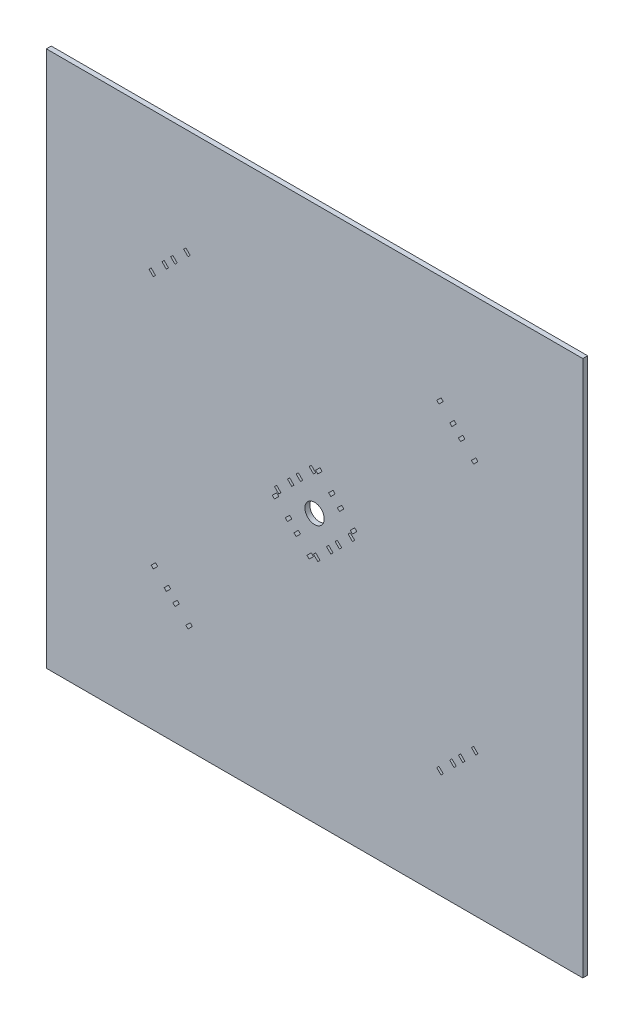
SolidWorks part; units mm, degrees
ref_plane "Front Plane" through (0, 0, 0) normal (0, 0, 1) x (1, 0, 0)
ref_plane "Top Plane" through (0, 0, 0) normal (0, 1, 0) x (1, 0, 0)
ref_plane "Right Plane" through (0, 0, 0) normal (1, 0, 0) x (0, 0, -1)
sketch "Model" plane through (0, 0, 0) normal (0, 0, 1) x (1, 0, 0)
  line L0 (0, 0) -> (0, 175)
  line L1 (0, 175) -> (175, 175)
  line L2 (175, 175) -> (175, 0)
  line L3 (175, 0) -> (0, 0)
  line L4 (139.3817, 47.6391) -> (140.7959, 46.2249)
  line L5 (140.7959, 46.2249) -> (140.0888, 45.5178)
  line L6 (140.0888, 45.5178) -> (138.6746, 46.932)
  line L7 (138.6746, 46.932) -> (139.3817, 47.6391)
  line L8 (135.1391, 43.3964) -> (136.5533, 41.9822)
  line L9 (136.5533, 41.9822) -> (135.8462, 41.2751)
  line L10 (135.8462, 41.2751) -> (134.432, 42.6893)
  line L11 (134.432, 42.6893) -> (135.1391, 43.3964)
  line L12 (132.3107, 40.568) -> (133.7249, 39.1538)
  line L13 (133.7249, 39.1538) -> (133.0178, 38.4467)
  line L14 (133.0178, 38.4467) -> (131.6036, 39.8609)
  line L15 (131.6036, 39.8609) -> (132.3107, 40.568)
  line L16 (128.068, 36.3254) -> (129.4822, 34.9112)
  line L17 (129.4822, 34.9112) -> (128.7751, 34.2041)
  line L18 (128.7751, 34.2041) -> (127.3609, 35.6183)
  line L19 (127.3609, 35.6183) -> (128.068, 36.3254)
  line L20 (87.8536, 76.5398) -> (89.2678, 75.1256)
  line L21 (89.2678, 75.1256) -> (88.5607, 74.4185)
  line L22 (88.5607, 74.4185) -> (87.1464, 75.8327)
  line L23 (87.1464, 75.8327) -> (87.8536, 76.5398)
  line L24 (92.0962, 80.7825) -> (93.5104, 79.3683)
  line L25 (93.5104, 79.3683) -> (92.8033, 78.6612)
  line L26 (92.8033, 78.6612) -> (91.3891, 80.0754)
  line L27 (91.3891, 80.0754) -> (92.0962, 80.7825)
  line L28 (47.6391, 35.6183) -> (46.2249, 34.2041)
  line L29 (46.2249, 34.2041) -> (45.5178, 34.9112)
  line L30 (45.5178, 34.9112) -> (46.932, 36.3254)
  line L31 (46.932, 36.3254) -> (47.6391, 35.6183)
  line L32 (43.3964, 39.8609) -> (41.9822, 38.4467)
  line L33 (41.9822, 38.4467) -> (41.2751, 39.1538)
  line L34 (41.2751, 39.1538) -> (42.6893, 40.568)
  line L35 (42.6893, 40.568) -> (43.3964, 39.8609)
  line L36 (40.568, 42.6893) -> (39.1538, 41.2751)
  line L37 (39.1538, 41.2751) -> (38.4467, 41.9822)
  line L38 (38.4467, 41.9822) -> (39.8609, 43.3964)
  line L39 (39.8609, 43.3964) -> (40.568, 42.6893)
  line L40 (36.3254, 46.932) -> (34.9112, 45.5178)
  line L41 (34.9112, 45.5178) -> (34.2041, 46.2249)
  line L42 (34.2041, 46.2249) -> (35.6183, 47.6391)
  line L43 (35.6183, 47.6391) -> (36.3254, 46.932)
  line L44 (75.8327, 86.4393) -> (74.4185, 85.0251)
  line L45 (74.4185, 85.0251) -> (73.7114, 85.7322)
  line L46 (73.7114, 85.7322) -> (75.1256, 87.1464)
  line L47 (75.1256, 87.1464) -> (75.8327, 86.4393)
  line L48 (80.0754, 82.1967) -> (78.6612, 80.7825)
  line L49 (78.6612, 80.7825) -> (77.9541, 81.4896)
  line L50 (77.9541, 81.4896) -> (79.3683, 82.9038)
  line L51 (79.3683, 82.9038) -> (80.0754, 82.1967)
  line L52 (82.9038, 79.3683) -> (81.4896, 77.9541)
  line L53 (81.4896, 77.9541) -> (80.7825, 78.6612)
  line L54 (80.7825, 78.6612) -> (82.1967, 80.0754)
  line L55 (82.1967, 80.0754) -> (82.9038, 79.3683)
  line L56 (87.1464, 75.1256) -> (85.7322, 73.7114)
  line L57 (85.7322, 73.7114) -> (85.0251, 74.4185)
  line L58 (85.0251, 74.4185) -> (86.4393, 75.8327)
  line L59 (86.4393, 75.8327) -> (87.1464, 75.1256)
  line L60 (101.2886, 89.2678) -> (99.8744, 87.8536)
  line L61 (99.8744, 87.8536) -> (99.1673, 88.5607)
  line L62 (99.1673, 88.5607) -> (100.5815, 89.9749)
  line L63 (100.5815, 89.9749) -> (101.2886, 89.2678)
  line L64 (97.0459, 93.5104) -> (95.6317, 92.0962)
  line L65 (95.6317, 92.0962) -> (94.9246, 92.8033)
  line L66 (94.9246, 92.8033) -> (96.3388, 94.2175)
  line L67 (96.3388, 94.2175) -> (97.0459, 93.5104)
  line L68 (94.2175, 96.3388) -> (92.8033, 94.9246)
  line L69 (92.8033, 94.9246) -> (92.0962, 95.6317)
  line L70 (92.0962, 95.6317) -> (93.5104, 97.0459)
  line L71 (93.5104, 97.0459) -> (94.2175, 96.3388)
  line L72 (89.9749, 100.5815) -> (88.5607, 99.1673)
  line L73 (88.5607, 99.1673) -> (87.8536, 99.8744)
  line L74 (87.8536, 99.8744) -> (89.2678, 101.2886)
  line L75 (89.2678, 101.2886) -> (89.9749, 100.5815)
  line L76 (129.4822, 140.0888) -> (128.068, 138.6746)
  line L77 (128.068, 138.6746) -> (127.3609, 139.3817)
  line L78 (127.3609, 139.3817) -> (128.7751, 140.7959)
  line L79 (128.7751, 140.7959) -> (129.4822, 140.0888)
  line L80 (133.7249, 135.8462) -> (132.3107, 134.432)
  line L81 (132.3107, 134.432) -> (131.6036, 135.1391)
  line L82 (131.6036, 135.1391) -> (133.0178, 136.5533)
  line L83 (133.0178, 136.5533) -> (133.7249, 135.8462)
  line L84 (136.5533, 133.0178) -> (135.1391, 131.6036)
  line L85 (135.1391, 131.6036) -> (134.432, 132.3107)
  line L86 (134.432, 132.3107) -> (135.8462, 133.7249)
  line L87 (135.8462, 133.7249) -> (136.5533, 133.0178)
  line L88 (140.7959, 128.7751) -> (139.3817, 127.3609)
  line L89 (139.3817, 127.3609) -> (138.6746, 128.068)
  line L90 (138.6746, 128.068) -> (140.0888, 129.4822)
  line L91 (140.0888, 129.4822) -> (140.7959, 128.7751)
  line L92 (94.9246, 83.6109) -> (96.3388, 82.1967)
  line L93 (96.3388, 82.1967) -> (95.6317, 81.4896)
  line L94 (95.6317, 81.4896) -> (94.2175, 82.9038)
  line L95 (94.2175, 82.9038) -> (94.9246, 83.6109)
  line L96 (99.1673, 87.8536) -> (100.5815, 86.4393)
  line L97 (100.5815, 86.4393) -> (99.8744, 85.7322)
  line L98 (99.8744, 85.7322) -> (98.4602, 87.1464)
  line L99 (98.4602, 87.1464) -> (99.1673, 87.8536)
  line L100 (75.1256, 89.2678) -> (76.5398, 87.8536)
  line L101 (76.5398, 87.8536) -> (75.8327, 87.1464)
  line L102 (75.8327, 87.1464) -> (74.4185, 88.5607)
  line L103 (74.4185, 88.5607) -> (75.1256, 89.2678)
  line L104 (79.3683, 93.5104) -> (80.7825, 92.0962)
  line L105 (80.7825, 92.0962) -> (80.0754, 91.3891)
  line L106 (80.0754, 91.3891) -> (78.6612, 92.8033)
  line L107 (78.6612, 92.8033) -> (79.3683, 93.5104)
  line L108 (82.1967, 96.3388) -> (83.6109, 94.9246)
  line L109 (83.6109, 94.9246) -> (82.9038, 94.2175)
  line L110 (82.9038, 94.2175) -> (81.4896, 95.6317)
  line L111 (81.4896, 95.6317) -> (82.1967, 96.3388)
  line L112 (86.4393, 100.5815) -> (87.8536, 99.1673)
  line L113 (87.8536, 99.1673) -> (87.1464, 98.4602)
  line L114 (87.1464, 98.4602) -> (85.7322, 99.8744)
  line L115 (85.7322, 99.8744) -> (86.4393, 100.5815)
  line L116 (34.2041, 130.1893) -> (35.6183, 128.7751)
  line L117 (35.6183, 128.7751) -> (34.9112, 128.068)
  line L118 (34.9112, 128.068) -> (33.497, 129.4822)
  line L119 (33.497, 129.4822) -> (34.2041, 130.1893)
  line L120 (38.4467, 134.432) -> (39.8609, 133.0178)
  line L121 (39.8609, 133.0178) -> (39.1538, 132.3107)
  line L122 (39.1538, 132.3107) -> (37.7396, 133.7249)
  line L123 (37.7396, 133.7249) -> (38.4467, 134.432)
  line L124 (41.2751, 137.2604) -> (42.6893, 135.8462)
  line L125 (42.6893, 135.8462) -> (41.9822, 135.1391)
  line L126 (41.9822, 135.1391) -> (40.568, 136.5533)
  line L127 (40.568, 136.5533) -> (41.2751, 137.2604)
  line L128 (45.5178, 141.503) -> (46.932, 140.0888)
  line L129 (46.932, 140.0888) -> (46.2249, 139.3817)
  line L130 (46.2249, 139.3817) -> (44.8107, 140.7959)
  line L131 (44.8107, 140.7959) -> (45.5178, 141.503)
  circle A0 centre (87.5, 87.5) radius 3.15
extrude "Boss-Extrude1" add sketch "Model" along normal blind 1.5875
